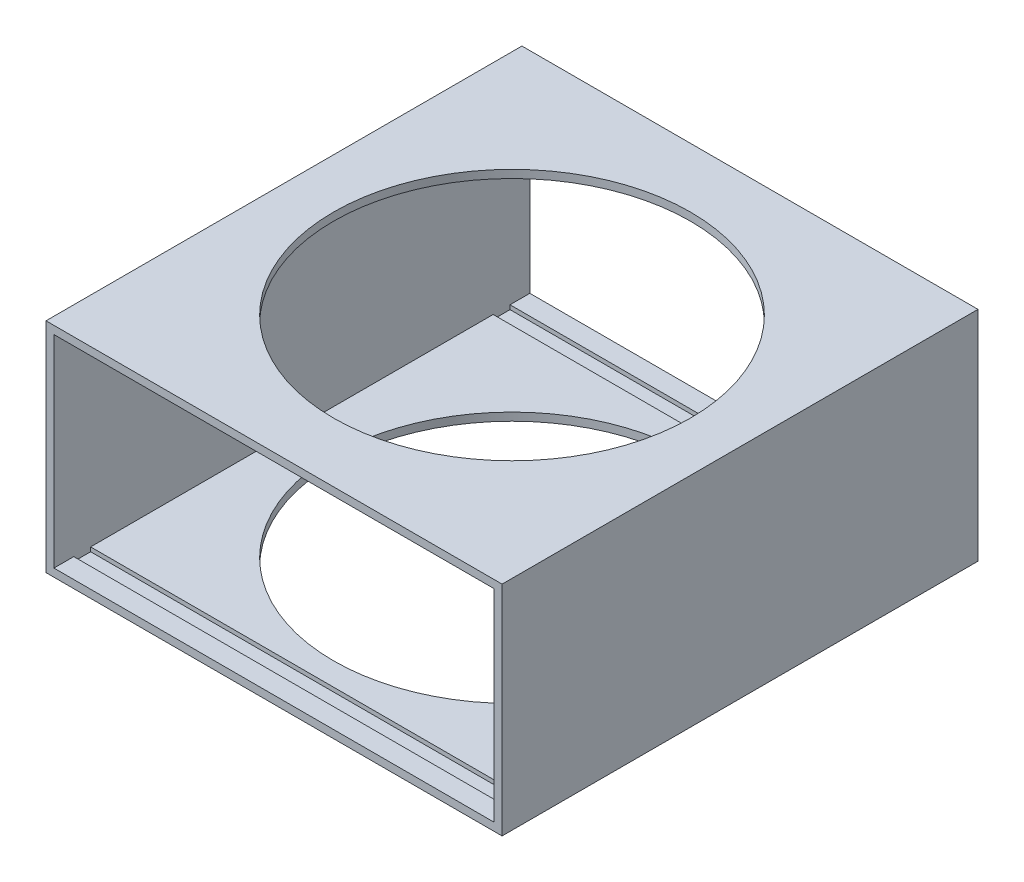
SolidWorks part; units mm, degrees
ref_plane "Front Plane" through (0, 0, 0) normal (0, 0, 1) x (1, 0, 0)
ref_plane "Top Plane" through (0, 0, 0) normal (0, 1, 0) x (1, 0, 0)
ref_plane "Right Plane" through (0, 0, 0) normal (1, 0, 0) x (0, 0, -1)
sketch "Edge" plane through (0, 0, 0) normal (0, 1, 0) x (1, 0, 0)
  line L0 (0, 0) -> (0, 280) construction
  point P4 (0, 80)
  point P5 (0, 200)
  point P7 (0, 140)
  dimension "D2" = 80
  dimension "D1" = 80
  dimension "D4" = 60
  dimension "D3" = 120
ref_plane "Plane1" through (0, 0, -80) normal (0, 0, -1) x (-1, 0, 0)
ref_plane "Plane3" through (0, 0, -200) normal (0, 0, -1) x (-1, 0, 0)
ref_plane "Plane4" through (0, 0, -280) normal (0, 0, -1) x (-1, 0, 0)
sketch "Sketch4" plane through (0, 0, -80) normal (0, 0, -1) x (-1, 0, 0)
  line L1 (-57.5, -27.5) -> (57.5, -27.5)
  line L2 (-57.5, -27.5) -> (-57.5, 27.5)
  line L3 (-57.5, 27.5) -> (57.5, 27.5)
  line L4 (57.5, -27.5) -> (57.5, 27.5)
  line L5 (-57.5, -27.5) -> (57.5, 27.5) construction
  line L6 (-57.5, 27.5) -> (57.5, -27.5) construction
  point P0 (0, 0)
  dimension "D1" = 115
  dimension "D2" = 55
extrude "Flat-surface" add sketch "Sketch4" along normal up to surface (120 mm away) thin up to plane "Plane3" thin type one direction reverse wall 2
ref_plane "Mid-plane" through (0, 0, -140) normal (0, 0, -1) x (-1, 0, 0)
sketch "Sketch9" plane through (0, 27.5, 0) normal (0, 1, 0) x (1, 0, 0)
  circle A0 centre (0, 140) radius 45
  dimension "D1" = 90
extrude "Cut-Extrude1" cut sketch "Sketch9" against normal up to surface (55 mm away) and the other way through all up to face at (0, -27.5, -140)
sketch "Sketch10" plane through (-55.5, 0, 0) normal (1, 0, 0) x (0, 0, -1)
  line L0 (200, 25.5) -> (80, 25.5) construction
  line L1 (85, 25.5) -> (85, 26.5639)
  line L2 (85, 26.5639) -> (89.2526, 26.5639)
  line L3 (89.2526, 26.5639) -> (89.2526, 25.5)
  line L4 (89.2526, 25.5) -> (85, 25.5)
  line L5 (80, 27.5) -> (80, -27.5) construction
  dimension "D1" = 5
extrude "Cut-Extrude2" cut sketch "Sketch10" along normal up to surface (111 mm away) up to face at (55.5, 0, -140)
mirror "Mirror1" about plane through (0, 0, 0) normal (0, 1, 0) of "Cut-Extrude2"
mirror "Mirror2" about plane through (0, 0, -140) normal (0, 0, -1) of "Mirror1", "Cut-Extrude2"
equation "\"inlet_diameter\"= 30"
equation "\"total_length\"=200"
equation "\"outlet_length\"=80"
equation "\"D2@Edge\"=\"outlet_length\""
equation "\"outlet_diameter\"= 50"
equation "\"side_length\"=115"
equation "\"inlet_lentgh\"=80"
equation "\"D1@Edge\"=\"inlet_lentgh\""
equation "\"flat_length\"=120"
equation "\"D4@Edge\"=\"flat_length\"/2"
equation "\"side_height\"=55"
equation "\"D1@Sketch4\"=\"side_length\""
equation "\"D2@Sketch4\"=\"side_height\""
equation "\"D3@Edge\"=\"flat_length\""
